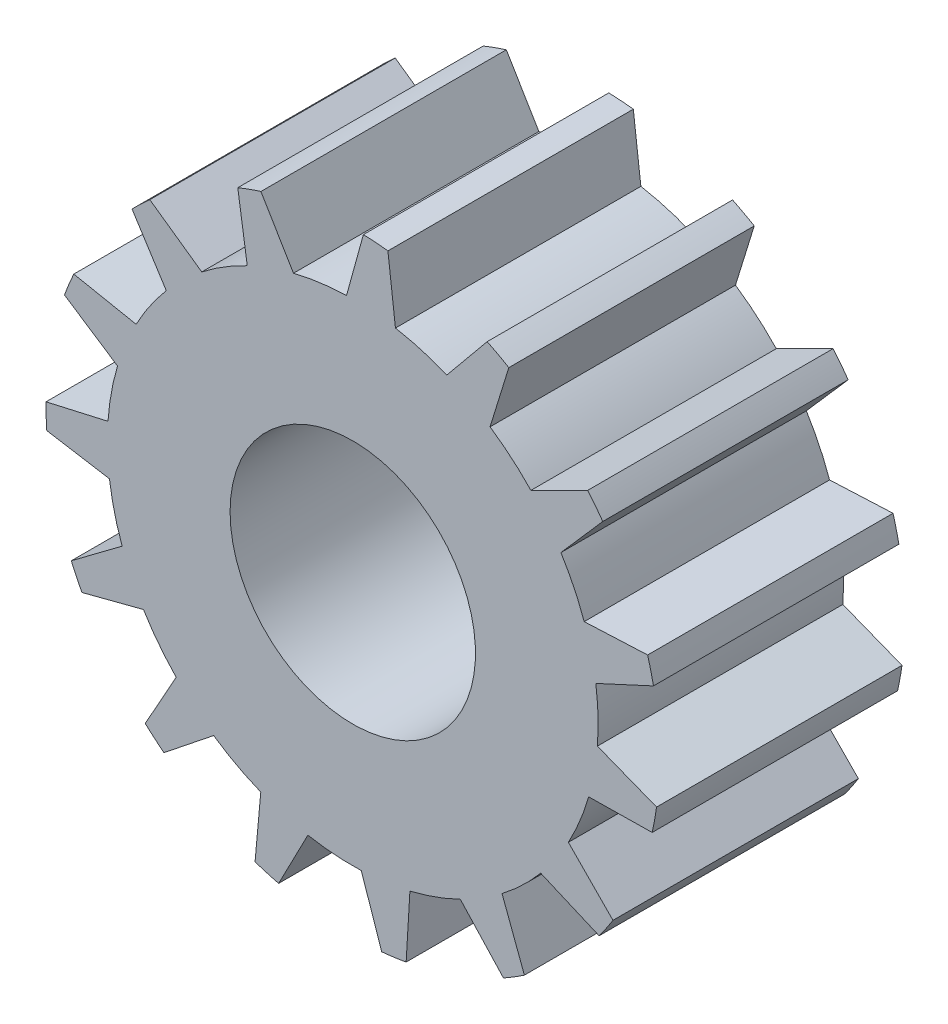
SolidWorks part; units mm, degrees
ref_plane "Front Plane" through (0, 0, 0) normal (0, 0, 1) x (1, 0, 0)
ref_plane "Top Plane" through (0, 0, 0) normal (0, 1, 0) x (1, 0, 0)
ref_plane "Right Plane" through (0, 0, 0) normal (1, 0, 0) x (0, 0, -1)
sketch "Sketch1" plane through (0, 0, 0) normal (0, 0, 1) x (1, 0, 0)
  circle A0 centre (0, 0) radius 5
  circle A1 centre (0, 0) radius 10
  dimension "D1" = 10
  dimension "D2" = 20
extrude "Boss-Extrude1" add sketch "Sketch1" along normal blind 10
sketch "Sketch2" plane through (0, 0, 0) normal (0, 0, -1) x (-1, 0, 0)
  circle A0 centre (0, 0) radius 12.5
  dimension "D1" = 25
extrude "Boss-Extrude2" add sketch "Sketch2" against normal blind 10
sketch "Sketch3" plane through (0, 0, 0) normal (0, 0, -1) x (-1, 0, 0)
  circle A0 centre (0, 0) radius 5
  dimension "D1" = 10
extrude "Cut-Extrude1" cut sketch "Sketch3" against normal blind 10
sketch "Sketch4" plane through (0, 0, 0) normal (0, 0, -1) x (-1, 0, 0)
  line L0 (-9.6697, 8.086) -> (-7.2581, 6.8789)
  line L1 (-5.5941, 8.2889) -> (-6.3906, 10.8649)
  line L2 (-5.5448, 11.3199) -> (-3.8327, 9.2364)
  line L3 (-1.739, 9.8476) -> (-1.4189, 12.5249)
  line L4 (-0.4612, 12.5966) -> (0.2554, 9.9967)
  line L5 (2.4167, 9.7036) -> (3.7981, 12.0192)
  line L6 (4.7021, 11.6951) -> (4.2994, 9.0286)
  line L7 (6.1546, 7.8817) -> (8.3584, 9.4353)
  line L8 (9.0525, 8.7715) -> (7.5999, 6.4993)
  line L9 (8.8283, 4.697) -> (11.4734, 5.2199)
  line L10 (11.8375, 4.3312) -> (9.5864, 2.8462)
  line L11 (9.9755, 0.7001) -> (12.6046, 0.1019)
  line L12 (12.5758, -0.858) -> (9.9153, -1.299)
  line L13 (9.3978, -3.4178) -> (11.5563, -5.0336)
  line L14 (11.1396, -5.8988) -> (8.5297, -5.2196)
  line L15 (7.1952, -6.9447) -> (8.5099, -9.2988)
  line L16 (7.7772, -9.9197) -> (5.6693, -8.2377)
  line L17 (3.7484, -9.2709) -> (3.992, -11.9562)
  line L18 (3.0701, -12.2254) -> (1.8286, -9.8314)
  line L19 (-0.3464, -9.994) -> (-1.2162, -12.5462)
  line L20 (-2.1678, -12.4172) -> (-2.3283, -9.7252)
  line L21 (-4.3814, -8.9891) -> (-6.214, -10.9669)
  line L22 (-7.0309, -10.4619) -> (-6.0826, -7.9374)
  line L23 (-7.6588, -6.4298) -> (-10.1374, -7.4913)
  line L24 (-10.6783, -6.6977) -> (-8.7851, -4.7772)
  line L25 (-9.6119, -2.7588) -> (-12.308, -2.7204)
  line L26 (-12.4794, -1.7754) -> (-9.9687, -0.7909)
  line L27 (-9.903, 1.3892) -> (-12.3504, 2.5209)
  line L68 (-12.1226, 3.4539) -> (-9.4285, 3.3321)
  line L71 (-8.4818, 5.297) -> (-10.2573, 7.3263)
  arc A0 (-8.4818, 5.297) -> (-9.4285, 3.3321) centre (0, 0) ccw
  arc A1 (-9.6697, 8.086) -> (-6.3906, 10.8649) centre (0, 0) cw
  arc A2 (-5.5941, 8.2889) -> (-7.2581, 6.8789) centre (0, 0) ccw
  arc A3 (-5.5448, 11.3199) -> (-1.4189, 12.5249) centre (0, 0) cw
  arc A4 (-1.739, 9.8476) -> (-3.8327, 9.2364) centre (0, 0) ccw
  arc A5 (-0.4612, 12.5966) -> (3.7981, 12.0192) centre (0, 0) cw
  arc A6 (2.4167, 9.7036) -> (0.2554, 9.9967) centre (0, 0) ccw
  arc A7 (4.7021, 11.6951) -> (8.3584, 9.4353) centre (0, 0) cw
  arc A8 (-12.1226, 3.4539) -> (-10.2573, 7.3263) centre (0, 0) cw
  arc A9 (6.1546, 7.8817) -> (4.2994, 9.0286) centre (0, 0) ccw
  arc A10 (9.0525, 8.7715) -> (11.4734, 5.2199) centre (0, 0) cw
  arc A11 (8.8283, 4.697) -> (7.5999, 6.4993) centre (0, 0) ccw
  arc A12 (11.8375, 4.3312) -> (12.6046, 0.1019) centre (0, 0) cw
  arc A13 (9.9755, 0.7001) -> (9.5864, 2.8462) centre (0, 0) ccw
  arc A14 (12.5758, -0.858) -> (11.5563, -5.0336) centre (0, 0) cw
  arc A15 (9.3978, -3.4178) -> (9.9153, -1.299) centre (0, 0) ccw
  arc A16 (11.1396, -5.8988) -> (8.5099, -9.2988) centre (0, 0) cw
  arc A17 (7.1952, -6.9447) -> (8.5297, -5.2196) centre (0, 0) ccw
  arc A18 (7.7772, -9.9197) -> (3.992, -11.9562) centre (0, 0) cw
  arc A19 (3.7484, -9.2709) -> (5.6693, -8.2377) centre (0, 0) ccw
  arc A20 (3.0701, -12.2254) -> (-1.2162, -12.5462) centre (0, 0) cw
  arc A21 (-0.3464, -9.994) -> (1.8286, -9.8314) centre (0, 0) ccw
  arc A22 (-2.1678, -12.4172) -> (-6.214, -10.9669) centre (0, 0) cw
  arc A23 (-4.3814, -8.9891) -> (-2.3283, -9.7252) centre (0, 0) ccw
  arc A24 (-7.0309, -10.4619) -> (-10.1374, -7.4913) centre (0, 0) cw
  arc A25 (-7.6588, -6.4298) -> (-6.0826, -7.9374) centre (0, 0) ccw
  arc A26 (-10.6783, -6.6977) -> (-12.308, -2.7204) centre (0, 0) cw
  arc A27 (-9.6119, -2.7588) -> (-8.7851, -4.7772) centre (0, 0) ccw
  arc A28 (-12.4794, -1.7754) -> (-12.3504, 2.5209) centre (0, 0) cw
  arc A29 (-9.903, 1.3892) -> (-9.9687, -0.7909) centre (0, 0) ccw
  point P62 (0, 0)
  point P123 (-10.185, 7.2467)
  point P130 (0, 0)
  dimension "D1" = 20
  dimension "D2" = 15
extrude "Cut-Extrude4" cut sketch "Sketch4" against normal blind 10
